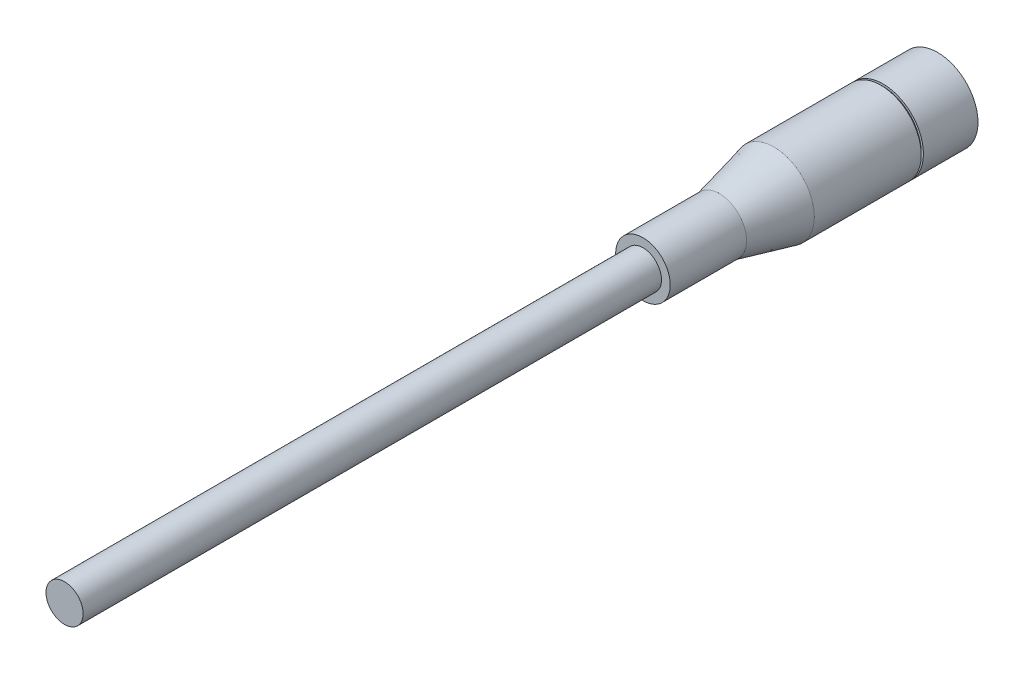
SolidWorks part; units mm, degrees
material "PP Copolymer"
ref_plane "Front Plane" through (0, 0, 0) normal (0, 0, 1) x (1, 0, 0)
ref_plane "Top Plane" through (0, 0, 0) normal (0, 1, 0) x (1, 0, 0)
ref_plane "Right Plane" through (0, 0, 0) normal (1, 0, 0) x (0, 0, -1)
sketch "S2D0001" plane through (0, 0, 0) normal (1, 0, 0) x (0, 0, -1)
  line L0 (0, 0) -> (0, 4.699)
  line L1 (0, 4.699) -> (-6.35, 4.699)
  line L2 (-6.35, 4.699) -> (-6.35, 4.445)
  line L3 (-6.35, 4.445) -> (-6.604, 4.445)
  line L4 (-6.604, 4.445) -> (-6.604, 4.699)
  line L5 (-6.604, 4.699) -> (-19.05, 4.699)
  line L6 (-19.05, 4.699) -> (-25.4, 3.175)
  line L7 (-25.4, 3.175) -> (-34.29, 3.175)
  line L8 (-34.29, 3.175) -> (-34.29, 0)
  line L9 (-34.29, 0) -> (0, 0)
  line L10 (-36.0045, 0) -> (1.7145, 0) construction
  dimension "D1" = 9.398
  dimension "D2" = 0.254
  dimension "D3" = 8.89
  dimension "D4" = 6.35
  dimension "D5" = 34.29
  dimension "D6" = 6.35
  dimension "D7" = 8.89
  dimension "D8" = 19.05
revolve "Revolve1" add sketch "S2D0001" angle 360 about L10
sketch "Sketch2" plane through (0, 0, 0) normal (0, 0, -1) x (-1, 0, 0)
  circle A0 centre (0, 0) radius 2.159
  circle A1 centre (0, 0) radius 4.699 construction
  dimension "D1" = 4.318
extrude "Extrude1" add sketch "Sketch2" against normal blind 101.6
sketch "Sketch4" plane through (0, 0, 0) normal (0, 0, -1) x (-1, 0, 0)
  circle A0 centre (0, 0) radius 3.937
  circle A1 centre (0, 0) radius 3.175
  circle A2 centre (0, 2.54) radius 0.381
  circle A3 centre (2.54, 0) radius 0.381
  circle A4 centre (-2.54, 0) radius 0.381
  circle A5 centre (0, 0) radius 4.699 construction
  circle A6 centre (0, 0) radius 2.54 construction
  dimension "D1" = 7.874
  dimension "D2" = 6.35
  dimension "D3" = 5.08
  dimension "D4" = 0.762
extrude "Cut-Extrude2" cut sketch "Sketch4" against normal blind 5.08
